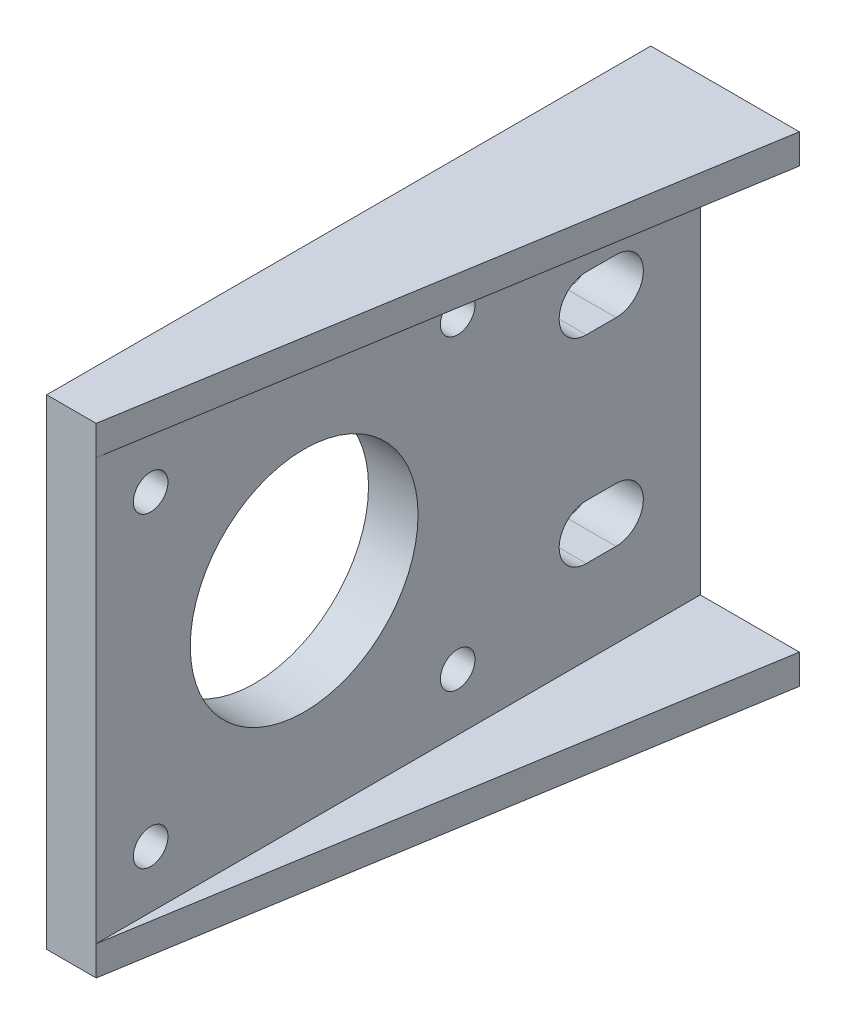
SolidWorks part; units mm, degrees
ref_plane "Front Plane" through (0, 0, 0) normal (0, 0, 1) x (1, 0, 0)
ref_plane "Top Plane" through (0, 0, 0) normal (0, 1, 0) x (1, 0, 0)
ref_plane "Right Plane" through (0, 0, 0) normal (1, 0, 0) x (0, 0, -1)
sketch "Sketch2" plane through (0, 0, 0) normal (1, 0, 0) x (0, 0, -1)
  line L0 (0, 0) -> (-21, 0) construction
  line L1 (-21, 0) -> (-21, -21.25) construction
  line L3 (-21, -21.25) -> (40, -21.25)
  line L4 (-21, -21.25) -> (-21, 21.25)
  line L5 (-21, 21.25) -> (40, 21.25)
  line L6 (40, -21.25) -> (40, 21.25)
  line L7 (30, 21.25) -> (30, -21.25) construction
  line L8 (28.5, 10) -> (31.5, 10) construction
  line L9 (28.5, 12.75) -> (31.5, 12.75)
  line L10 (28.5, 7.25) -> (31.5, 7.25)
  line L11 (28.5, -10) -> (31.5, -10) construction
  line L12 (28.5, -12.75) -> (31.5, -12.75)
  line L13 (28.5, -7.25) -> (31.5, -7.25)
  circle A0 centre (0, 0) radius 11.5
  circle A1 centre (-15.5, 15.5) radius 1.75
  circle A2 centre (15.5, -15.5) radius 1.75
  circle A3 centre (15.5, 15.5) radius 1.75
  circle A4 centre (-15.5, -15.5) radius 1.75
  arc A5 (28.5, 12.75) -> (28.5, 7.25) centre (28.5, 10) ccw
  arc A6 (31.5, 7.25) -> (31.5, 12.75) centre (31.5, 10) ccw
  arc A7 (28.5, -12.75) -> (28.5, -7.25) centre (28.5, -10) cw
  arc A8 (31.5, -7.25) -> (31.5, -12.75) centre (31.5, -10) cw
  point P21 (30, 10)
  point P28 (30, -10)
  dimension "D1" = 23
  dimension "D7" = 15.5
  dimension "D8" = 3.5
  dimension "D9" = 3.5
  dimension "D10" = 15.5
  dimension "D13" = 5.5
  dimension "D15" = 15.5
  dimension "D6" = 15.5
  dimension "D2" = 21
  dimension "D3" = 21.25
  dimension "D4" = 42.5
  dimension "D5" = 61
  dimension "D11" = 10
  dimension "D12" = 10
  dimension "D14" = 3
extrude "Boss-Extrude2" add sketch "Sketch2" along normal blind 5
sketch "Sketch4" plane through (0, -21.25, 0) normal (0, -1, 0) x (1, 0, 0)
  line L0 (0, -40) -> (15, -40)
  line L1 (15, -40) -> (5, 21)
  line L2 (5, 21) -> (0, 21)
  line L3 (0, 21) -> (0, -40)
  dimension "D1" = 15
extrude "Boss-Extrude3" add sketch "Sketch4" along normal blind 3
pattern_linear "LPattern1" count 2 spacing 45.5 along (0, 1, 0) of "Boss-Extrude3"
